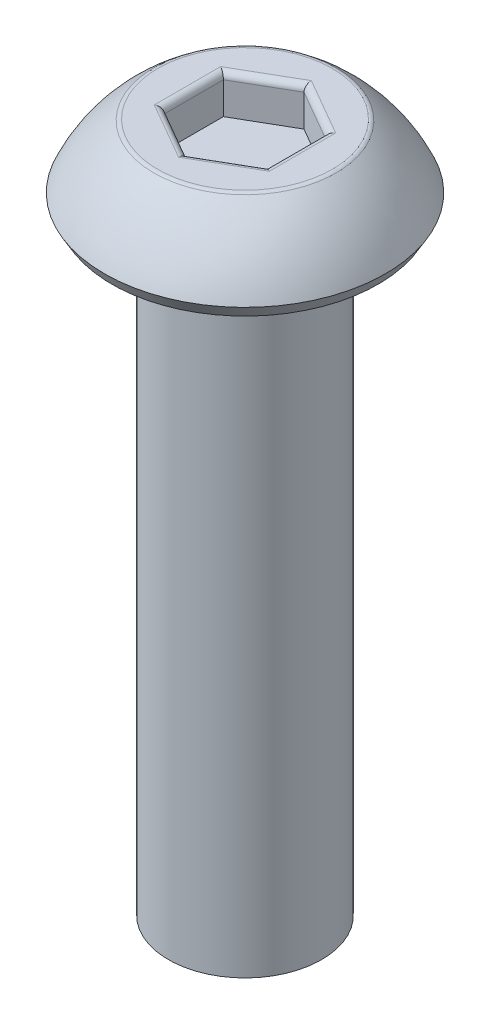
SolidWorks part; units mm, degrees
ref_plane "Front Plane" through (0, 0, 0) normal (0, 0, 1) x (1, 0, 0)
ref_plane "Top Plane" through (0, 0, 0) normal (0, 1, 0) x (1, 0, 0)
ref_plane "Right Plane" through (0, 0, 0) normal (1, 0, 0) x (0, 0, -1)
sketch "Sketch1" plane through (0, 0, 0) normal (1, 0, 0) x (0, 0, -1)
  line L0 (0, 0) -> (0, 1.5) construction
  line L1 (0, 1.5) -> (-1.75, 1.5)
  line L3 (-2.75, 0.25) -> (-2.6057, 0)
  line L4 (-2.6057, 0) -> (-1.5, 0)
  line L5 (-1.5, 0) -> (-1.5, -12)
  line L6 (-1.5, -12) -> (0, -12)
  line L7 (0, -12) -> (0, 1.5)
  line L8 (0, 0) -> (-1.5, 0) construction
  arc A0 (-1.75, 1.5) -> (-2.75, 0.25) centre (0.0077, -0.9312) ccw
  dimension "D5" = 3
  dimension "D1" = 1.5
  dimension "D2" = 2.75
  dimension "D3" = 1.75
  dimension "D4" = 0.25
  dimension "D6" = 60
  dimension "D7" = 1.5
  dimension "D8" = 12
revolve "Revolve1" add sketch "Sketch1" angle 360 about L7
sketch "Sketch2" plane through (0, 1.5, 0) normal (0, 1, 0) x (1, 0, 0)
  line L1 (0, 1.1547) -> (-1, 0.5774)
  line L2 (-1, 0.5774) -> (-1, -0.5774)
  line L3 (-1, -0.5774) -> (0, -1.1547)
  line L4 (0, -1.1547) -> (1, -0.5774)
  line L5 (1, -0.5774) -> (1, 0.5774)
  line L6 (1, 0.5774) -> (0, 1.1547)
  circle A0 centre (0, 0) radius 1 construction
  dimension "D1" = 2
extrude "Cut-Extrude1" cut sketch "Sketch2" against normal blind 0.75
fillet "Fillet1" radius 0.125 7 edges at (0, 1.5, -1.75) (-0.5, 1.5, 0.866) (0.5, 1.5, 0.866) (1, 1.5, 0) (0.5, 1.5, -0.866) (-0.5, 1.5, -0.866) (-1, 1.5, 0)
